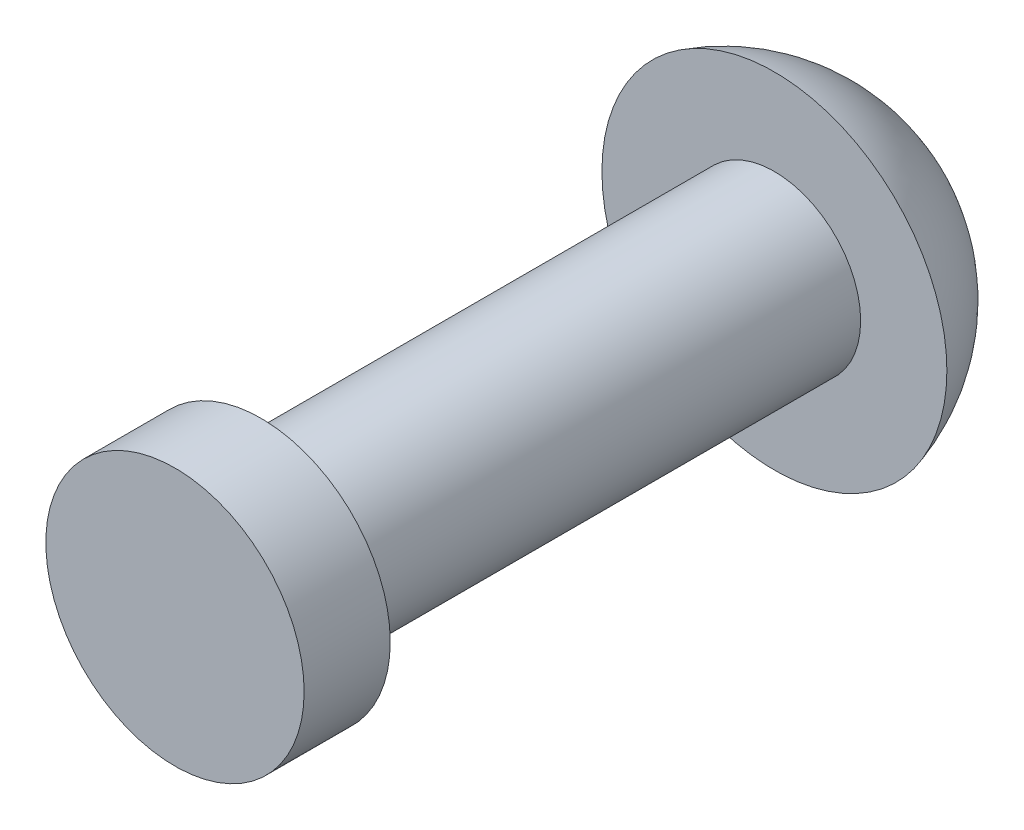
SolidWorks part; units mm, degrees
material "6061 Alloy"
ref_plane "Plane1" through (0, 0, 0) normal (0, 0, 1) x (1, 0, 0)
ref_plane "Plane2" through (0, 0, 0) normal (0, 1, 0) x (1, 0, 0)
ref_plane "Plane3" through (0, 0, 0) normal (1, 0, 0) x (0, 0, -1)
sketch "Sketch1" plane through (0, 0, 0) normal (0, 0, 1) x (1, 0, 0)
  circle A0 centre (0, 0) radius 1.9844
  dimension "Diameter" = 3.9688
extrude "Ext Shank" add sketch "Sketch1" along normal blind 13.7922
sketch "Sketch2" plane through (0, 0, 0) normal (0, 1, 0) x (1, 0, 0)
  line L2 (0, -13.7922) -> (0, 0) construction
  line L3 (0, 2.9718) -> (0, 0)
  line L4 (0, 0) -> (3.9688, 0)
  line L5 (3.9688, 0) -> (-3.9688, 0) construction
  line L6 (-3.9688, 0) -> (-3.9688, 9.6833) construction
  line L7 (0, 0) -> (0, 24.2412) construction
  arc A0 (0, 2.9718) -> (3.9688, 0) centre (0, -1.1642) cw
  dimension "Head Dia" = 7.9375
  dimension "Head Thick" = 2.9718
revolve "Rev Head" add sketch "Sketch2" angle 360 about L7
sketch "Sketch3" plane through (0, 0, 13.7922) normal (0, 0, 1) x (1, 0, 0)
  circle A0 centre (0, 0) radius 2.9718
  dimension "D1" = 5.9436
extrude "Ext Clinch" add sketch "Sketch3" against normal offset from surface (1.9812 mm away) 11.811 up to face at (3.9688, 0, 0)
fillet "Fillet1" [suppressed] radius 0.127
